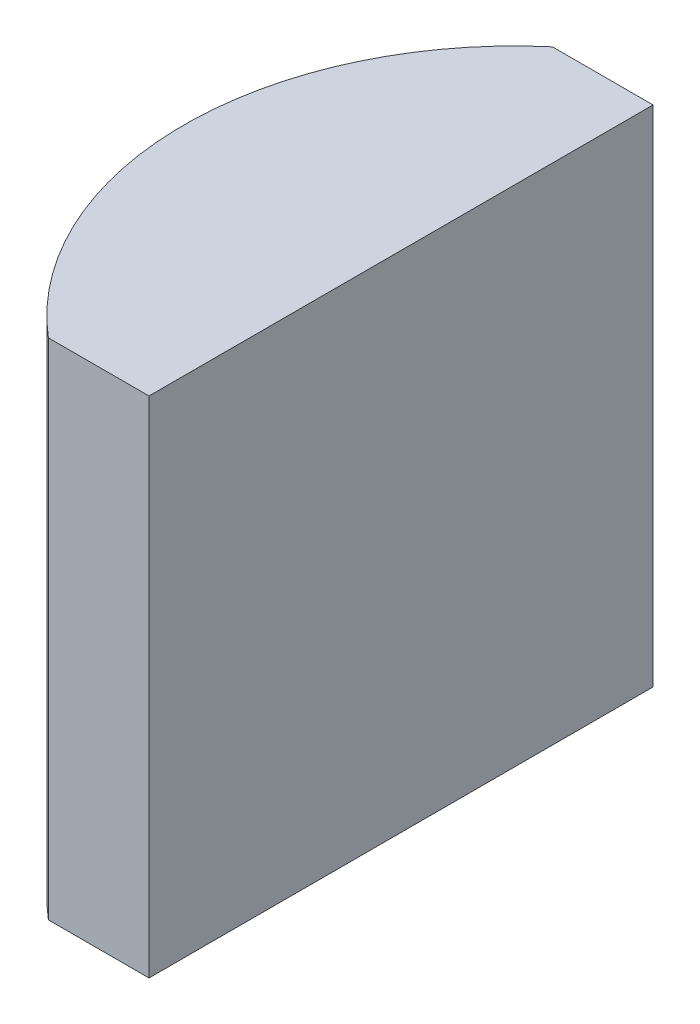
SolidWorks part; units mm, degrees
ref_plane "前视基准面" through (0, 0, 0) normal (0, 0, 1) x (1, 0, 0)
ref_plane "上视基准面" through (0, 0, 0) normal (0, 1, 0) x (1, 0, 0)
ref_plane "右视基准面" through (0, 0, 0) normal (1, 0, 0) x (0, 0, -1)
sketch "草图1" plane through (0, 0, 0) normal (0, 1, 0) x (1, 0, 0)
  line L0 (-4.6849, 0) -> (10.8051, 0) construction
  line L1 (0.1086, 5) -> (2.1052, 5)
  line L2 (0.1086, -5) -> (2.1052, -5)
  line L3 (2.1052, 5) -> (2.1052, -5)
  arc A0 (0.1086, 5) -> (0.1086, -5) centre (4.3552, 0) ccw
  point P2 (-2.2048, 0)
  point P4 (2.1052, 0)
  point P8 (0, 0)
  point P10 (10.8051, 0)
  point P11 (0, 0)
  point P12 (0, 0)
  point P13 (-4.6849, 0)
  dimension "D2" = 5
  dimension "D3" = 6.56
  dimension "D4" = 4.31
  dimension "D1" = 5
extrude "凸台-拉伸1" add sketch "草图1" along normal blind 10
